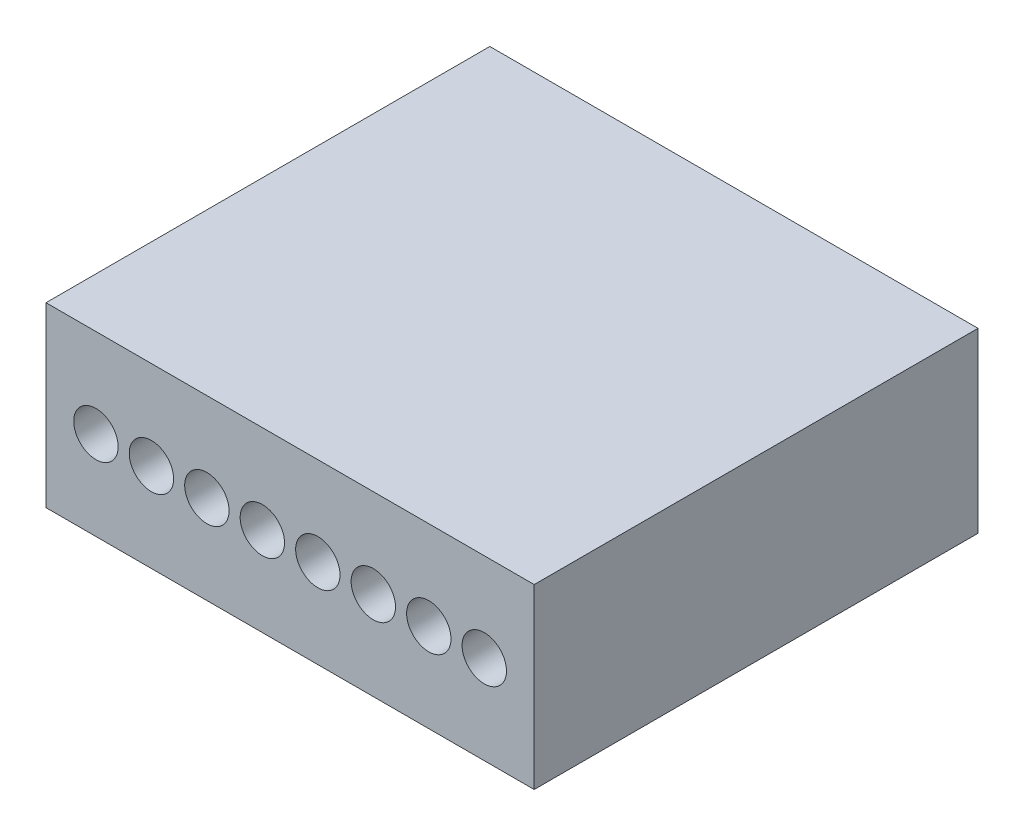
SolidWorks part; units mm, degrees
ref_plane "Front Plane" through (0, 0, 0) normal (0, 0, 1) x (1, 0, 0)
ref_plane "Top Plane" through (0, 0, 0) normal (0, 1, 0) x (1, 0, 0)
ref_plane "Right Plane" through (0, 0, 0) normal (1, 0, 0) x (0, 0, -1)
sketch "Sketch2" plane through (0, 0, 0) normal (0, 0, 1) x (1, 0, 0)
  line L1 (0, 0) -> (11, 0)
  line L2 (0, 0) -> (0, 4)
  line L3 (0, 4) -> (11, 4)
  line L4 (11, 0) -> (11, 4)
  dimension "D1" = 11
  dimension "D2" = 4
extrude "Boss-Extrude1" add sketch "Sketch2" along normal blind 10
sketch "Sketch3" plane through (0, 0, 10) normal (0, 0, 1) x (1, 0, 0)
  line L0 (0, 2) -> (11, 2) construction
  line L1 (0, 4) -> (0, 0) construction
  line L2 (11, 0) -> (11, 4) construction
  line L3 (0, 2) -> (11, 2) construction
  line L4 (11, 4) -> (0, 4) construction
  line L5 (0, 0) -> (11, 0) construction
  line L6 (1.125, 4) -> (1.125, 0) construction
  circle A0 centre (1.125, 2) radius 0.5
  circle A1 centre (2.375, 2) radius 0.5
  circle A2 centre (3.625, 2) radius 0.5
  circle A3 centre (4.875, 2) radius 0.5
  circle A4 centre (6.125, 2) radius 0.5
  circle A5 centre (7.375, 2) radius 0.5
  circle A6 centre (8.625, 2) radius 0.5
  circle A7 centre (9.875, 2) radius 0.5
  circle A21 centre (24.875, 2) radius 0.5 [skipped]
  circle A22 centre (23.625, 2) radius 0.5 [skipped]
  circle A23 centre (22.375, 2) radius 0.5 [skipped]
  circle A24 centre (21.125, 2) radius 0.5 [skipped]
  circle A25 centre (19.875, 2) radius 0.5 [skipped]
  circle A26 centre (18.625, 2) radius 0.5 [skipped]
  circle A27 centre (17.375, 2) radius 0.5 [skipped]
  circle A28 centre (16.125, 2) radius 0.5 [skipped]
  circle A29 centre (14.875, 2) radius 0.5 [skipped]
  circle A30 centre (13.625, 2) radius 0.5 [skipped]
  circle A31 centre (12.375, 2) radius 0.5 [skipped]
  circle A32 centre (11.125, 2) radius 0.5 [skipped]
  dimension "D1" = 1
  dimension "D2" = 2
  dimension "D3" = 1.125
  dimension "D5" = 1.25
  dimension "D4" = 20
extrude "Cut-Extrude1" cut sketch "Sketch3" against normal blind 5
sketch "Sketch4" plane through (0, 0, 10) normal (0, 0, 1) x (1, 0, 0)
  point P0 (1.125, 2)
  point P1 (2.375, 2)
  point P3 (3.625, 2)
  point P5 (4.875, 2)
  point P7 (6.125, 2)
  point P9 (7.375, 2)
  point P11 (8.625, 2)
  point P13 (9.875, 2)
  point P17 (0, 0)
  point P27 (0, 0)
  point P37 (0, 0)
